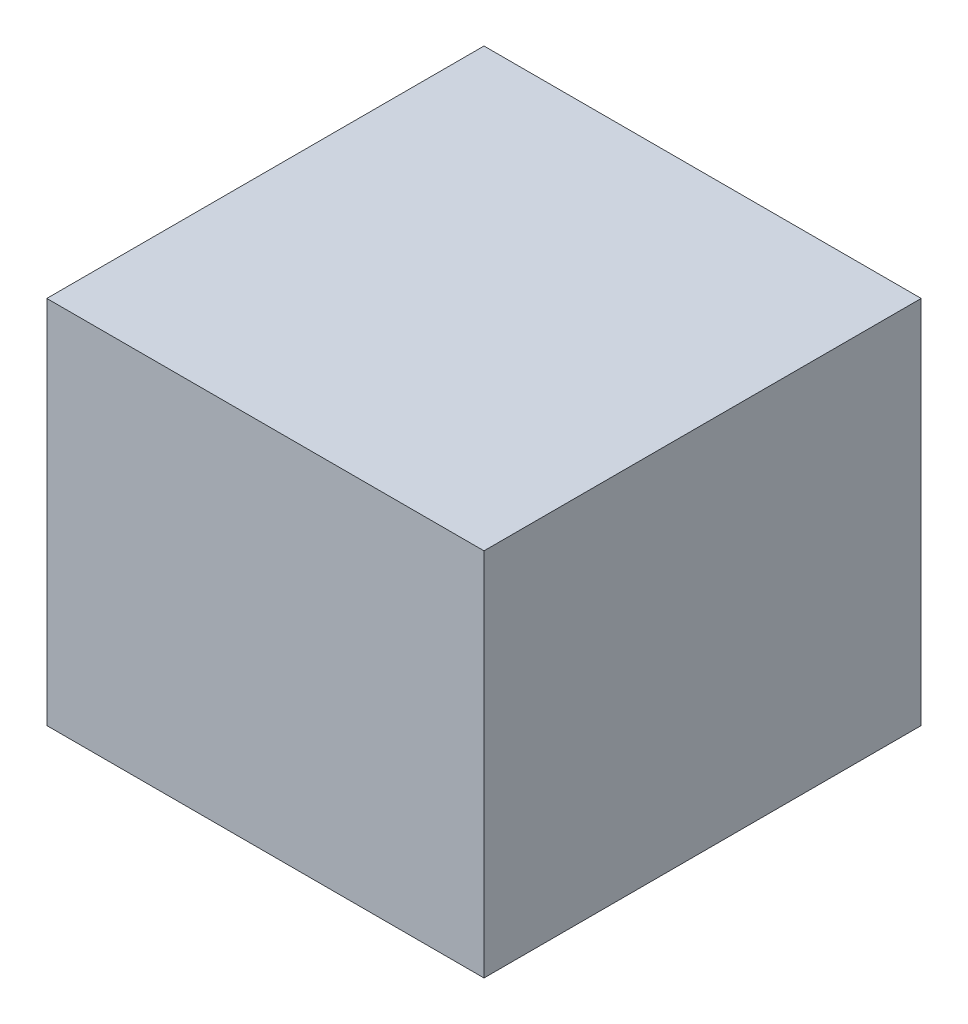
SolidWorks part; units mm, degrees
ref_plane "Front Plane" through (0, 0, 0) normal (0, 0, 1) x (1, 0, 0)
ref_plane "Top Plane" through (0, 0, 0) normal (0, 1, 0) x (1, 0, 0)
ref_plane "Right Plane" through (0, 0, 0) normal (1, 0, 0) x (0, 0, -1)
sketch "Sketch1" plane through (0, 0, 0) normal (0, 1, 0) x (1, 0, 0)
  line L1 (-165.1, 165.1) -> (165.1, 165.1)
  line L2 (-165.1, 165.1) -> (-165.1, -165.1)
  line L3 (-165.1, -165.1) -> (165.1, -165.1)
  line L4 (165.1, 165.1) -> (165.1, -165.1)
  line L5 (-165.1, 165.1) -> (165.1, -165.1) construction
  line L6 (-165.1, -165.1) -> (165.1, 165.1) construction
  point P0 (0, 0)
  dimension "D1" = 330.2
  dimension "D2" = 330.2
extrude "Boss-Extrude1" add sketch "Sketch1" along normal blind 279.4
